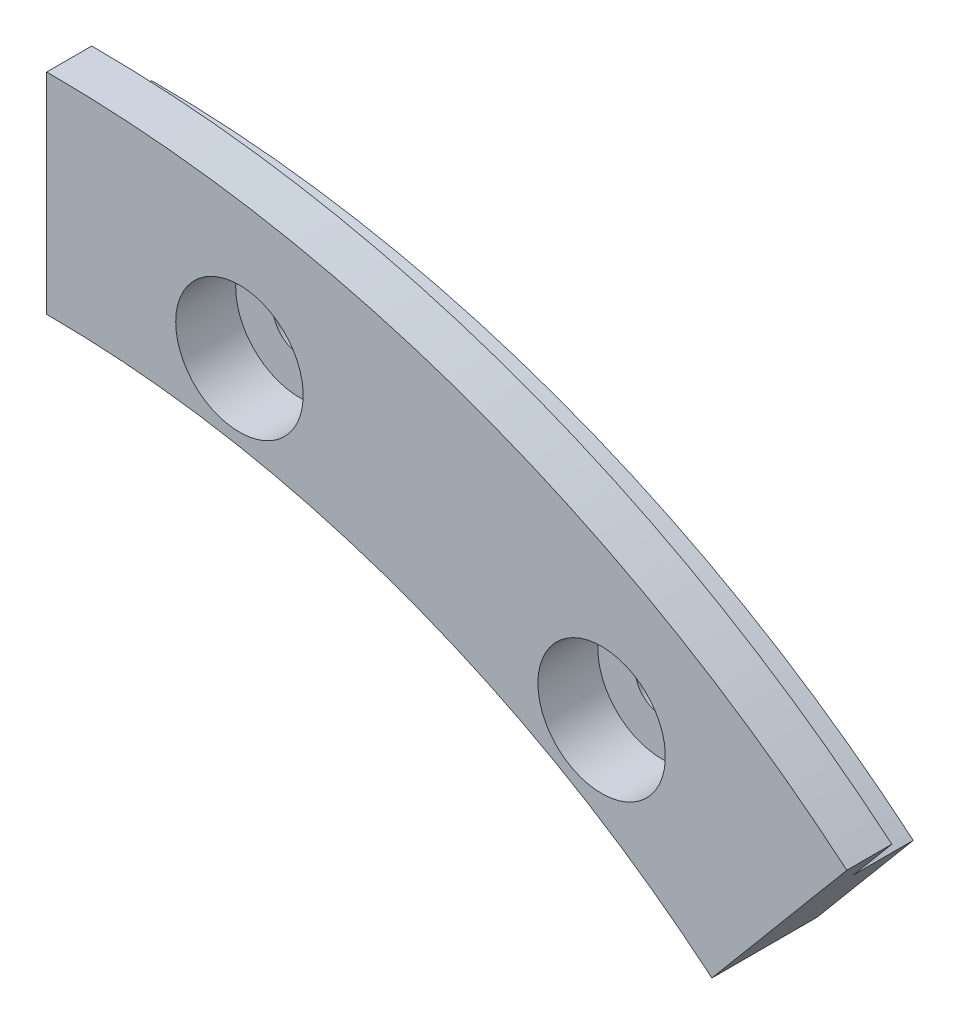
SolidWorks part; units mm, degrees
ref_plane "Front Plane" through (0, 0, 0) normal (0, 0, 1) x (1, 0, 0)
ref_plane "Top Plane" through (0, 0, 0) normal (0, 1, 0) x (1, 0, 0)
ref_plane "Right Plane" through (0, 0, 0) normal (1, 0, 0) x (0, 0, -1)
sketch "Sketch1" plane through (0, 0, 0) normal (0, 0, 1) x (1, 0, 0)
  line L0 (0, 79) -> (0, 0) construction
  line L1 (0, 0) -> (50.7802, 60.5175) construction
  line L2 (0, 79) -> (0, 69)
  line L3 (44.3523, 52.8571) -> (50.7802, 60.5175)
  arc A0 (0, 79) -> (50.7802, 60.5175) centre (0, 0) cw
  arc A1 (0, 69) -> (44.3523, 52.8571) centre (0, 0) cw
  dimension "D1" = 79
  dimension "D2" = 40
  dimension "D3" = 10
extrude "Boss-Extrude1" add sketch "Sketch1" along normal blind 4
sketch "Sketch2" plane through (0, 0, 4) normal (0, 0, 1) x (1, 0, 0)
  line L0 (44.3523, 52.8571) -> (50.7802, 60.5175) construction
  line L1 (0, 79) -> (0, 69) construction
  line L2 (44.3523, 52.8571) -> (53.3514, 63.5817)
  line L3 (0, 83) -> (0, 69)
  arc A0 (44.3523, 52.8571) -> (0, 69) centre (0, 0) ccw construction
  arc A1 (44.3523, 52.8571) -> (0, 69) centre (0, 0) ccw
  arc A4 (53.3514, 63.5817) -> (0, 83) centre (0, 0) ccw
  arc A5 (53.3514, 63.5817) -> (0, 83) centre (0, 0) ccw
  point P3 (0, 82.6209)
  point P5 (53.0075, 63.1719)
  dimension "D1" = 4
extrude "Boss-Extrude2" add sketch "Sketch2" along normal blind 3
sketch "Sketch4" plane through (0, 0, 7) normal (0, 0, 1) x (1, 0, 0)
  line L0 (12.85, 72.8758) -> (0, 0) construction
  line L1 (0, 0) -> (37, 64.0859) construction
  line L2 (0, 74) -> (0, 0) construction
  circle A1 centre (12.85, 72.8758) radius 1.75
  arc A2 (47.5663, 56.6873) -> (0, 74) centre (0, 0) ccw
  arc A3 (47.5663, 56.6873) -> (0, 74) centre (0, 0) ccw construction
  circle A4 centre (37, 64.0859) radius 1.75
  dimension "D4" = 3.5
  dimension "D5" = 74
  dimension "D2" = 10
  dimension "D3" = 20
  dimension "D1" = 5
extrude "Cut-Extrude1" cut sketch "Sketch4" against normal through all
sketch "Sketch5" plane through (0, 0, 7) normal (0, 0, -1) x (-1, 0, 0)
  circle A10 centre (-37, 64.0859) radius 4.25
  circle A11 centre (-37, 64.0859) radius 4.25
  circle A13 centre (-12.85, 72.8758) radius 4.25
  circle A14 centre (-12.85, 72.8758) radius 4.25
  dimension "D1" = 2.5
  dimension "D2" = 2.5
extrude "Cut-Extrude2" cut sketch "Sketch5" along normal blind 4
